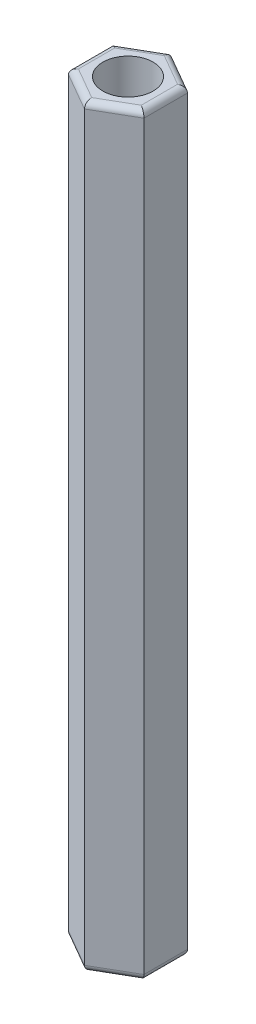
SolidWorks part; units mm, degrees
ref_plane "前视基准面" through (0, 0, 0) normal (0, 0, 1) x (1, 0, 0)
ref_plane "上视基准面" through (0, 0, 0) normal (0, 1, 0) x (1, 0, 0)
ref_plane "右视基准面" through (0, 0, 0) normal (1, 0, 0) x (0, 0, -1)
sketch "草图1" plane through (0, 0, 0) normal (0, 1, 0) x (1, 0, 0)
  line L1 (3, -1.7321) -> (3, 1.7321)
  line L2 (3, 1.7321) -> (0, 3.4641)
  line L3 (0, 3.4641) -> (-3, 1.7321)
  line L4 (-3, 1.7321) -> (-3, -1.7321)
  line L5 (-3, -1.7321) -> (0, -3.4641)
  line L6 (0, -3.4641) -> (3, -1.7321)
  circle A0 centre (0, 0) radius 3 construction
  circle A1 centre (0, 0) radius 2
  dimension "D2" = 4
  dimension "D1" = 6
extrude "凸台-拉伸1" add sketch "草图1" along normal blind 60
fillet "圆角1" radius 0.5 12 edges at (-1.5, 60, 2.5981) (-3, 60, 0) (-1.5, 60, -2.5981) (1.5, 60, -2.5981) (3, 60, 0) (1.5, 60, 2.5981) (-1.5, 0, 2.5981) (1.5, 0, 2.5981) (3, 0, 0) (1.5, 0, -2.5981) (-1.5, 0, -2.5981) (-3, 0, 0)
